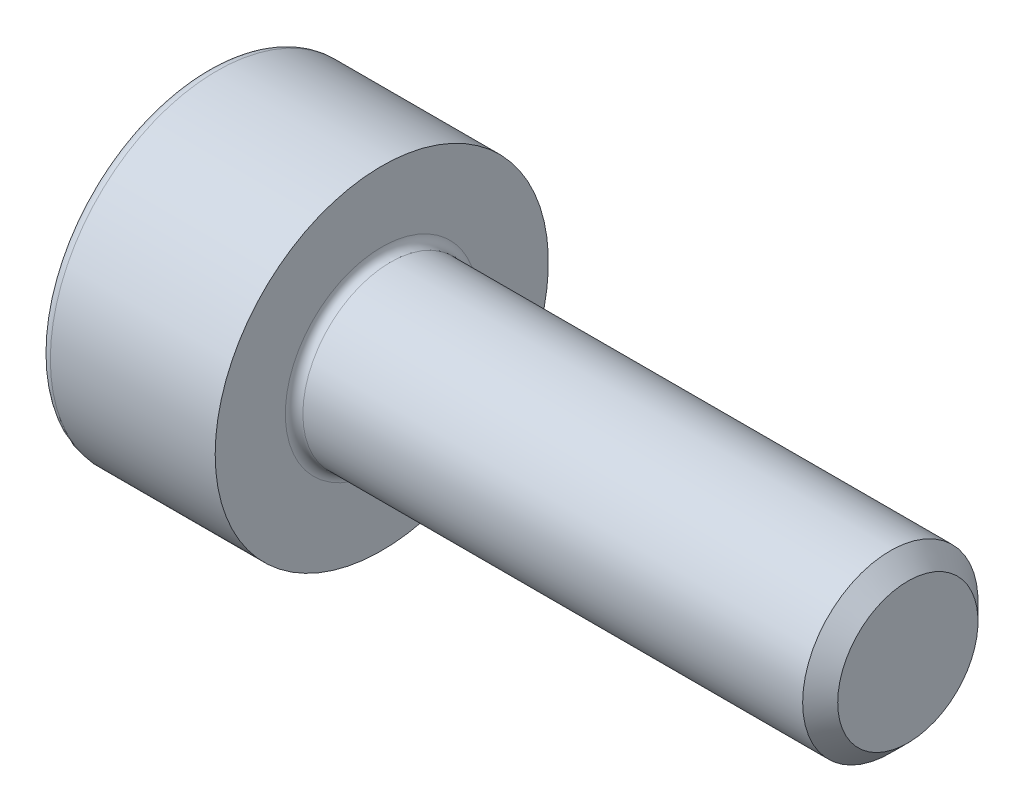
SolidWorks part; units mm, degrees
material "AISI Тип A2 Инструментальная сталь"
ref_plane "Front Plane" through (0, 0, 0) normal (0, 0, 1) x (1, 0, 0)
ref_plane "Top Plane" through (0, 0, 0) normal (0, 1, 0) x (1, 0, 0)
ref_plane "Right Plane" through (0, 0, 0) normal (1, 0, 0) x (0, 0, -1)
sketch "Sketch1" plane through (0, 0, 0) normal (0, 0, 1) x (1, 0, 0)
  line L0 (0, 0) -> (0, 1.9)
  line L1 (0, 1.9) -> (2, 1.9)
  line L2 (2, 1.9) -> (2, 0)
  line L3 (0, 0) -> (4.2799, 0) construction
  line L4 (2, 0) -> (8, 0)
  line L5 (8, 0) -> (8, 1)
  line L6 (8, 1) -> (2, 1)
  dimension "D1" = 6
  dimension "D2" = 2
  dimension "D3" = 1.9
  dimension "D4" = 1
revolve "Revolve1" add sketch "Sketch1" angle 360 about L3
fillet "Fillet1" radius 0.1 1 edges at (2, 0, 1)
fillet "Fillet2" radius 0.12 1 edges at (0, 0, 1.9)
chamfer "Chamfer1" distance 0.2 angle 45 1 edges at (8, 0, 1)
sketch "Sketch2" plane through (0, 0, 0) normal (-1, 0, 0) x (0, 0, 1)
  line L1 (0, 0.866) -> (-0.75, 0.433)
  line L2 (-0.75, 0.433) -> (-0.75, -0.433)
  line L3 (-0.75, -0.433) -> (0, -0.866)
  line L4 (0, -0.866) -> (0.75, -0.433)
  line L5 (0.75, -0.433) -> (0.75, 0.433)
  line L6 (0.75, 0.433) -> (0, 0.866)
  circle A0 centre (0, 0) radius 0.75 construction
  dimension "D1" = 1.5
extrude "Extrude1" cut sketch "Sketch2" against normal blind 1
